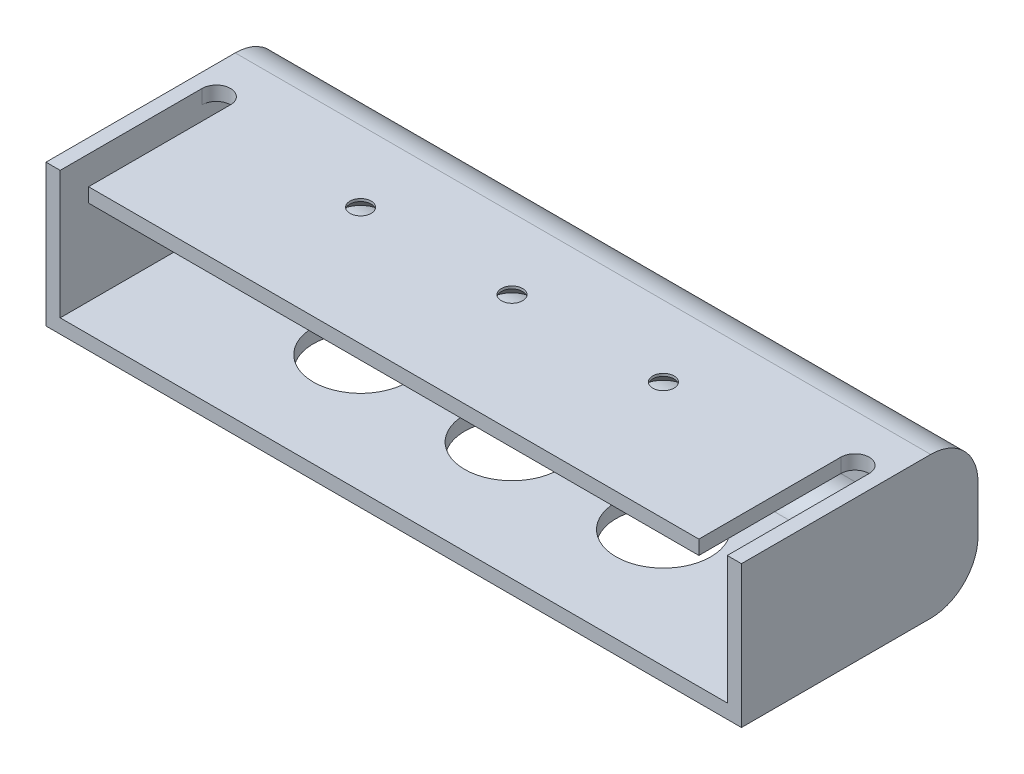
SolidWorks part; units mm, degrees
ref_plane "Front Plane" through (0, 0, 0) normal (0, 0, 1) x (1, 0, 0)
ref_plane "Top Plane" through (0, 0, 0) normal (0, 1, 0) x (1, 0, 0)
ref_plane "Right Plane" through (0, 0, 0) normal (1, 0, 0) x (0, 0, -1)
sketch "Sketch1" plane through (0, 0, 0) normal (0, 1, 0) x (1, 0, 0)
  line L1 (-73.5, 25) -> (73.5, 25)
  line L2 (-73.5, 25) -> (-73.5, -25)
  line L3 (-73.5, -25) -> (73.5, -25)
  line L4 (73.5, 25) -> (73.5, -25)
  line L5 (-73.5, 25) -> (73.5, -25) construction
  line L6 (-73.5, -25) -> (73.5, 25) construction
  point P0 (0, 0)
  dimension "D1" = 147
  dimension "D2" = 50
extrude "Boss-Extrude1" add sketch "Sketch1" along normal blind 30
fillet "Fillet1" radius 10 2 edges at (0, 30, -25) (0, 0, -25)
shell "Shell1" thickness 3
sketch "Sketch2" plane through (0, 30, 0) normal (0, 1, 0) x (1, 0, 0)
  line L0 (-70.5, -25) -> (-70.5, 5)
  line L1 (-73.5, -25) -> (73.5, -25) construction
  line L2 (-70.5, -25) -> (-64.5, -25)
  line L3 (-64.5, -25) -> (-64.5, 5)
  line L4 (-70.5, 15) -> (-70.5, -25) construction
  arc A0 (-64.5, 5) -> (-70.5, 5) centre (-67.5, 5) ccw
  dimension "D1" = 30
  dimension "D2" = 6
extrude "Cut-Extrude1" cut sketch "Sketch2" against normal up to next (3 mm away)
mirror "Mirror1" about plane through (0, 0, 0) normal (1, 0, 0) of "Cut-Extrude1"
hole_wizard "CSK for M4 Countersunk Flat Head Screw1" positions "Sketch4" profile "Sketch3" countersink size "M4" standard "ISO" end condition through all
sketch "Sketch4" plane through (0, 27, 0) normal (0, -1, 0) x (-1, 0, 0)
  line L0 (0, 0) -> (-50000, 0) construction
  line L1 (0, 0) -> (0, 50000) construction
  point P0 (32, 0)
  point P2 (0, 0)
  point P4 (-32, 0)
  dimension "D1" = 64
sketch "Sketch3" plane through (-32, 27, 0) normal (1, 0, 0) x (0, 0, -1)
  line L0 (0, 0) -> (0, 3)
  line L1 (0, 3) -> (2.25, 3)
  line L2 (2.25, 3) -> (2.25, 2.45)
  line L3 (2.25, 2.45) -> (4.7, 0)
  line L5 (4.7, 0) -> (0, 0)
  line L6 (-2.25, 2.45) -> (-4.7, 0) construction
  line L11 (0, -6.35) -> (0, 107.95) construction
  dimension "Thru Hole Dia." = 4.5
  dimension "Thru Hole Depth" = 3
  dimension "Near C'Sink Dia." = 9.4
  dimension "Near C'Sink Angle" = 90
sketch "Sketch5" plane through (0, 0, 0) normal (0, -1, 0) x (1, 0, 0)
  circle A0 centre (0, 0) radius 10
  circle A1 centre (-32, 0) radius 10
  circle A2 centre (32, 0) radius 10
  circle A3 centre (32, 0) radius 2.25 construction
  circle A4 centre (0, 0) radius 2.25 construction
  circle A5 centre (-32, 0) radius 2.25 construction
  dimension "D1" = 20
extrude "Cut-Extrude2" cut sketch "Sketch5" against normal up to next
